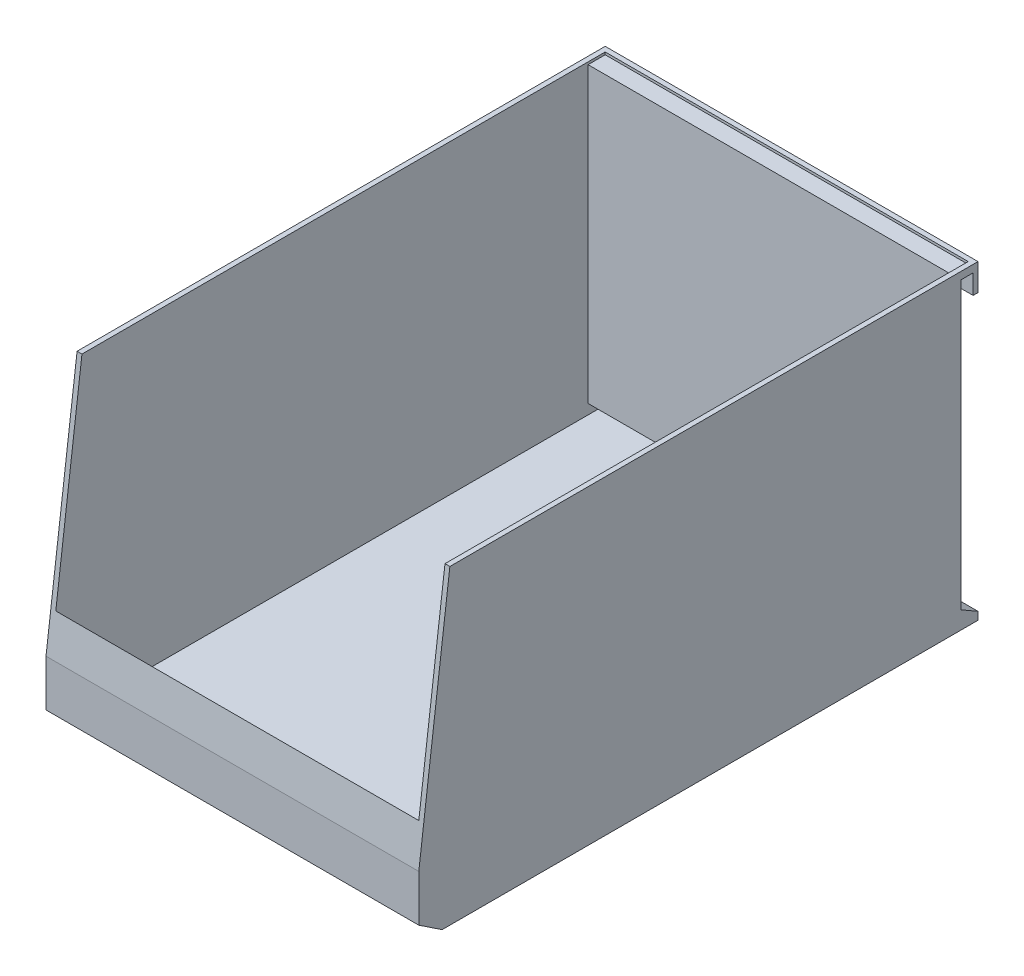
SolidWorks part; units mm, degrees
ref_plane "Front Plane" through (0, 0, 0) normal (0, 0, 1) x (1, 0, 0)
ref_plane "Top Plane" through (0, 0, 0) normal (0, 1, 0) x (1, 0, 0)
ref_plane "Right Plane" through (0, 0, 0) normal (1, 0, 0) x (0, 0, -1)
sketch "Sketch1" plane through (0, 0, 0) normal (0, 1, 0) x (1, 0, 0)
  line L1 (-76.2, -114.3) -> (76.2, -114.3)
  line L2 (-76.2, -114.3) -> (-76.2, 114.3)
  line L3 (-76.2, 114.3) -> (76.2, 114.3)
  line L4 (76.2, -114.3) -> (76.2, 114.3)
  line L5 (-76.2, -114.3) -> (76.2, 114.3) construction
  line L6 (-76.2, 114.3) -> (76.2, -114.3) construction
  point P0 (0, 0)
  dimension "D1" = 228.6
  dimension "D2" = 152.4
extrude "Boss-Extrude1" add sketch "Sketch1" along normal blind 127
sketch "Sketch2" plane through (76.2, 0, 0) normal (1, 0, 0) x (0, 0, -1)
  line L0 (-101.6, 127) -> (-114.3, 25.4)
  line L1 (-114.3, 127) -> (114.3, 127) construction
  line L2 (-114.3, 127) -> (-114.3, 0) construction
  line L3 (-114.3, 6.35) -> (-114.3, 0)
  line L4 (-114.3, 6.35) -> (-104.775, 0)
  line L5 (-114.3, 0) -> (114.3, 0) construction
  line L6 (-114.3, 0) -> (-104.775, 0)
  line L7 (-114.3, 25.4) -> (-114.3, 127)
  line L8 (-114.3, 127) -> (-101.6, 127)
  dimension "D1" = 12.7
  dimension "D2" = 9.525
  dimension "D3" = 19.05
  dimension "D4" = 6.35
extrude "Cut-Extrude1" cut sketch "Sketch2" against normal through all
sketch "Sketch3" plane through (76.2, 0, 0) normal (1, 0, 0) x (0, 0, -1)
  line L0 (114.3, 127) -> (114.3, 0) construction
  line L1 (114.3, 7.2165) -> (107.3, 7.2165) construction
  line L3 (114.3, 116) -> (107.3, 116) construction
  line L4 (107.3, 7.2165) -> (107.3, 116)
  line L5 (107.3, 7.2165) -> (114.3, 3.175)
  line L6 (107.3, 116) -> (107.3, 124)
  line L7 (107.3, 124) -> (112.3, 124)
  line L8 (112.3, 124) -> (112.3, 116)
  line L9 (112.3, 116) -> (114.3, 116)
  line L10 (114.3, 116) -> (114.3, 3.175)
  line L11 (-101.6, 127) -> (114.3, 127) construction
  dimension "D1" = 7
  dimension "D2" = 3.175
  dimension "D3" = 30
  dimension "D4" = 2
  dimension "D5" = 3
  dimension "D6" = 8
extrude "Cut-Extrude2" cut sketch "Sketch3" against normal through all
shell "Shell1" thickness 2
